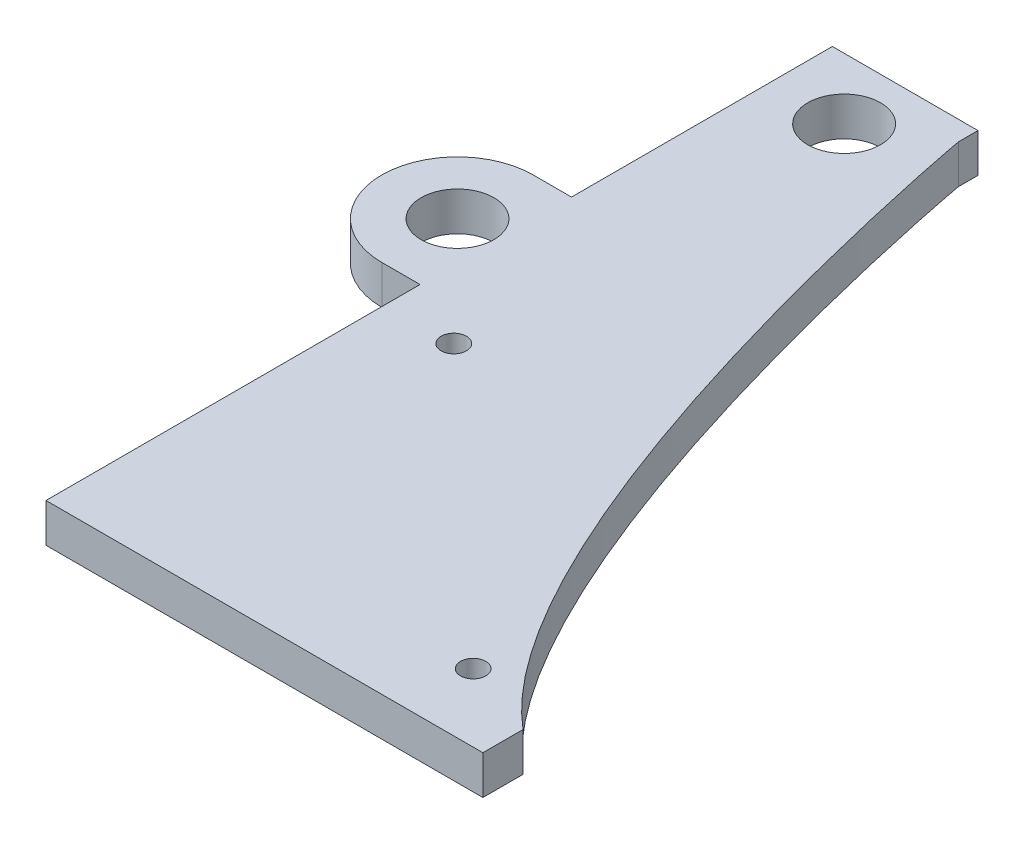
SolidWorks part; units mm, degrees
ref_plane "Front Plane" through (0, 0, 0) normal (0, 0, 1) x (1, 0, 0)
ref_plane "Top Plane" through (0, 0, 0) normal (0, 1, 0) x (1, 0, 0)
ref_plane "Right Plane" through (0, 0, 0) normal (1, 0, 0) x (0, 0, -1)
sketch "Sketch1" plane through (0, 0, 0) normal (0, 1, 0) x (1, 0, 0)
  line L0 (9.525, -53.975) -> (60.325, -53.975) construction
  line L1 (-9.525, -53.975) -> (9.525, -53.975) construction
  line L2 (-9.525, -53.975) -> (-9.525, 53.975) construction
  line L3 (-9.525, 53.975) -> (9.525, 53.975)
  line L4 (9.525, -53.975) -> (9.525, 53.975) construction
  line L5 (-9.525, -53.975) -> (9.525, 53.975) construction
  line L6 (-9.525, 53.975) -> (9.525, -53.975) construction
  line L7 (0, 53.975) -> (0, 45.9867) construction
  line L8 (-9.525, 50.7492) -> (9.525, 50.7492) construction
  line L9 (9.525, 51.435) -> (9.525, 53.975)
  line L10 (60.325, -53.975) -> (60.325, -48.895) construction
  line L11 (60.325, -48.895) -> (-9.525, -48.895) construction
  line L12 (60.325, -53.975) -> (60.325, -48.895) construction
  line L13 (60.325, -48.895) -> (-9.525, -48.895)
  line L14 (-9.525, -48.895) -> (-9.525, 53.975)
  line L15 (31.115, -19.685) -> (31.115, -48.895) construction
  circle A0 centre (0, 45.9867) radius 4.7625
  spline S0 degree 3 poles (9.525, 51.435) (9.525, 51.2145) (27.8191, -48.895) (60.325, -48.895) knots 0 0 0 0 1 1 1 1
  point P4 (0, 0)
  dimension "D5" = 9.525
  dimension "D1" = 107.95
  dimension "D2" = 19.05
  dimension "D3" = 50.8
  dimension "D4" = 2.54
  dimension "D6" = 104.7242
  dimension "D7" = 5.08
  dimension "D8" = 40.64
  dimension "D9" = 29.21
extrude "Boss-Extrude1" add sketch "Sketch1" along normal blind 5.08
sketch "Sketch4" plane through (0, 5.08, 0) normal (0, 1, 0) x (1, 0, 0)
  line L0 (-9.525, 53.975) -> (-9.525, -48.895) construction
  line L1 (60.325, -48.895) -> (41.275, -48.895)
  line L2 (60.325, -48.895) -> (60.325, -53.975)
  line L3 (60.325, -53.975) -> (41.275, -53.975)
  line L4 (41.275, -48.895) -> (41.275, -53.975)
  line L5 (60.325, -48.895) -> (41.275, -53.975) construction
  line L6 (60.325, -53.975) -> (41.275, -48.895) construction
  point P4 (50.8, -51.435)
  dimension "D1" = 50.8
  dimension "D2" = 5.08
extrude "Boss-Extrude2" add sketch "Sketch4" against normal up to surface (5.08 mm away) up to face at (17.145, 0, -2.286)
sketch "Sketch5" plane through (0, 0, 0) normal (0, -1, 0) x (1, 0, 0)
  circle A2 centre (-0.635, 4.445) radius 1.6607
  circle A5 centre (37.465, 40.005) radius 1.651
extrude "Cut-Extrude1" cut sketch "Sketch5" against normal through all both
sketch "Sketch6" plane through (0, 0, 0) normal (0, -1, 0) x (1, 0, 0)
  line L0 (-9.525, -9.9436) -> (-14.5359, -9.9436) construction
  line L1 (-9.525, -53.975) -> (-9.525, 48.895) construction
  line L2 (-14.5359, -0.0376) -> (-9.525, -0.0376)
  line L3 (-14.5359, -19.8496) -> (-9.525, -19.8496)
  line L4 (-9.525, -0.0376) -> (-9.525, -1.3984)
  line L5 (-9.525, -19.8496) -> (-9.525, -18.4887)
  line L6 (41.275, 53.975) -> (60.325, 53.975) construction
  circle A0 centre (-14.5359, -9.9436) radius 4.7625
  arc A1 (-9.525, -18.4887) -> (-9.525, -1.3984) centre (-14.5359, -9.9436) ccw
  arc A2 (-14.5359, -0.0376) -> (-14.5359, -19.8496) centre (-14.5359, -9.9436) ccw
  dimension "D1" = 63.9186
  dimension "D2" = 5.0109
extrude "Boss-Extrude3" add sketch "Sketch6" against normal blind 5.08
sketch "Sketch8" plane through (0, 5.08, 0) normal (0, 1, 0) x (1, 0, 0)
  circle A0 centre (-14.5359, 9.9436) radius 4.7625
sketch "Sketch9" plane through (0, 0, 0) normal (0, -1, 0) x (1, 0, 0)
  line L0 (60.325, 53.975) -> (60.325, 48.895) construction
  line L1 (60.325, 53.975) -> (60.325, 48.895)
  line L2 (41.275, 53.975) -> (60.325, 53.975) construction
  line L3 (41.275, 53.975) -> (60.325, 53.975)
  line L4 (41.275, 48.895) -> (41.275, 53.975) construction
  line L5 (41.275, 48.895) -> (41.275, 53.975)
  line L6 (41.275, 48.895) -> (47.625, 48.895)
  line L7 (47.625, 48.895) -> (47.625, 43.6465)
  line L8 (47.625, 48.895) -> (60.325, 48.895) construction
  spline S0 degree 3 poles (403.6577, -2926.3388) (28.4253, 3438.6609) (-194.6007, -3446.0355) (275.8334, 2936.2968) knots -2.047356 -2.047356 -2.047356 -2.047356 3.051792 3.051792 3.051792 3.051792 only from (60.325, 48.895) to (9.525, -51.435) construction
  spline S1 degree 3 poles (60.325, 48.895) (55.8144, 48.895) (51.5774, 46.9674) (47.625, 43.6465) knots 0 0 0 0 0.138763 0.138763 0.138763 0.138763
  dimension "D1" = 12.7
extrude "Cut-Extrude2" cut sketch "Sketch9" against normal through all both and the other way through all
